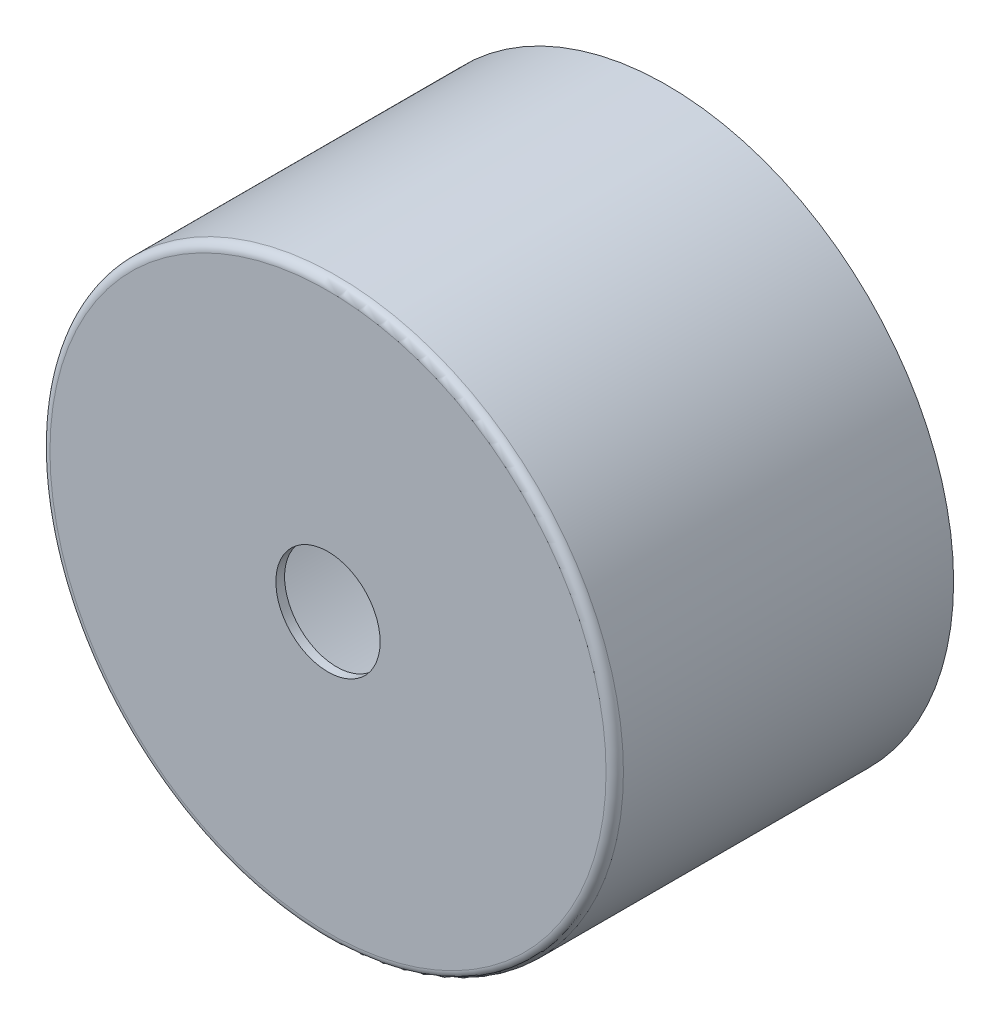
SolidWorks part; units mm, degrees
ref_plane "Front Plane" through (0, 0, 0) normal (0, 0, 1) x (1, 0, 0)
ref_plane "Top Plane" through (0, 0, 0) normal (0, 1, 0) x (1, 0, 0)
ref_plane "Right Plane" through (0, 0, 0) normal (1, 0, 0) x (0, 0, -1)
sketch "Sketch1" plane through (0, 0, 0) normal (0, 0, 1) x (1, 0, 0)
  circle A0 centre (0, 0) radius 16.5
  dimension "D1" = 33
extrude "Boss-Extrude1" add sketch "Sketch1" against normal blind 19.5
shell "Shell1" thickness 0.5
sketch "Sketch2" plane through (0, 0, 0) normal (0, 0, 1) x (1, 0, 0)
  circle A0 centre (0, 0) radius 3
  dimension "D1" = 6
extrude "Cut-Extrude1" cut sketch "Sketch2" against normal through all
fillet "Fillet1" radius 0.5 1 edges at (16.5, 0, 0)
